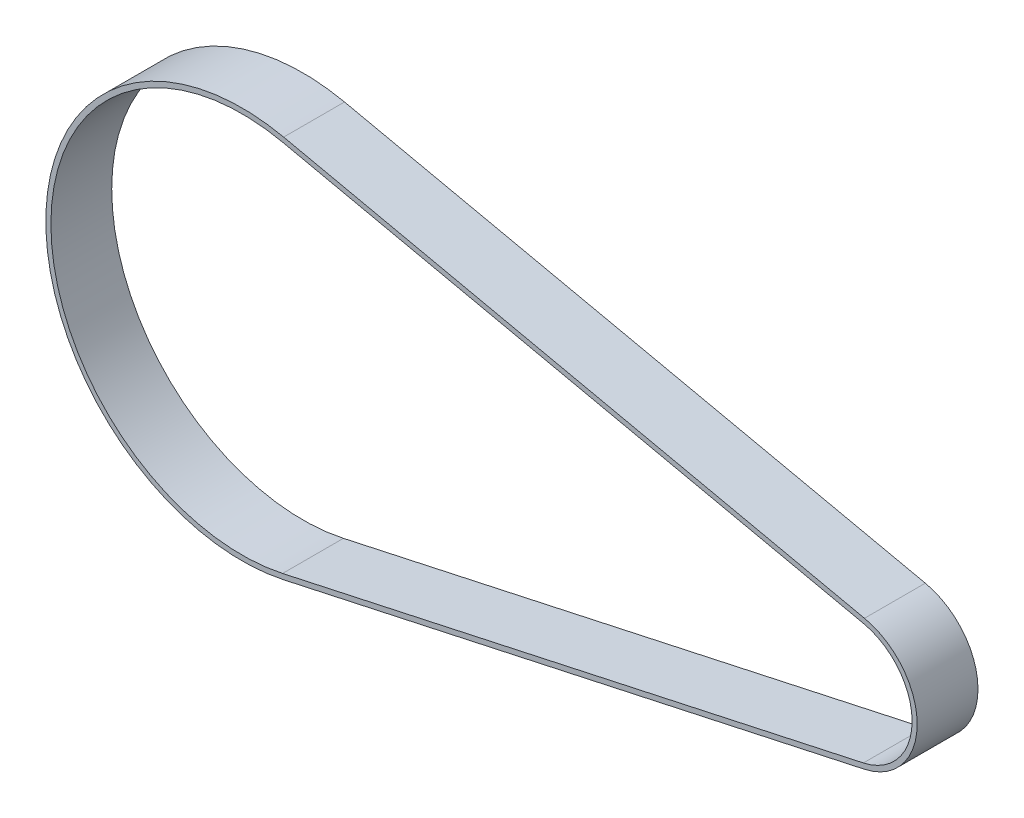
SolidWorks part; units mm, degrees
material "Caucho"
ref_plane "Alzado" through (0, 0, 0) normal (0, 0, 1) x (1, 0, 0)
ref_plane "Planta" through (0, 0, 0) normal (0, 1, 0) x (1, 0, 0)
ref_plane "Vista lateral" through (0, 0, 0) normal (1, 0, 0) x (0, 0, -1)
sketch "Croquis1" plane through (0, 0, 0) normal (0, 0, 1) x (1, 0, 0)
  line L0 (4.0056, 18.4195) -> (61.2962, 5.9607)
  line L1 (0, 0) -> (79.1587, 0) construction
  line L2 (61.2962, -5.9607) -> (4.0056, -18.4195)
  line L3 (61.4025, -6.4493) -> (4.1119, -18.9081)
  line L4 (4.1119, 18.9081) -> (61.4025, 6.4493)
  arc A0 (4.0056, 18.4195) -> (4.0056, -18.4195) centre (0, 0) ccw
  arc A1 (61.2962, -5.9607) -> (61.2962, 5.9607) centre (60, 0) ccw
  arc A2 (4.1119, 18.9081) -> (4.1119, -18.9081) centre (0, 0) ccw
  arc A3 (61.4025, -6.4493) -> (61.4025, 6.4493) centre (60, 0) ccw
  dimension "D1" = 12.2
  dimension "D2" = 37.7
  dimension "D3" = 60
  dimension "D4" = 0.5
extrude "Saliente-Extruir1" add sketch "Croquis1" along normal blind 6
